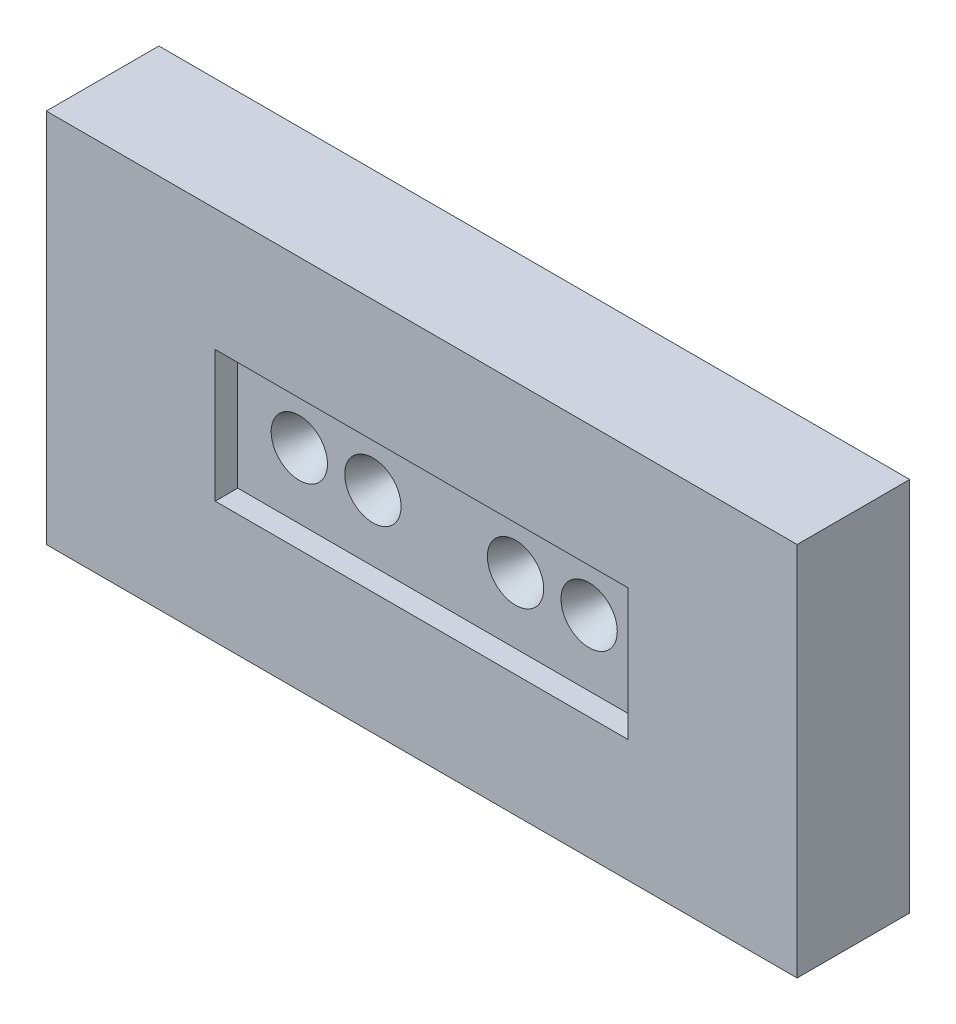
SolidWorks part; units mm, degrees
ref_plane "Front Plane" through (0, 0, 0) normal (0, 0, 1) x (1, 0, 0)
ref_plane "Top Plane" through (0, 0, 0) normal (0, 1, 0) x (1, 0, 0)
ref_plane "Right Plane" through (0, 0, 0) normal (1, 0, 0) x (0, 0, -1)
sketch "Sketch1" plane through (0, 0, 0) normal (0, 0, 1) x (1, 0, 0)
  line L1 (-20, 10) -> (20, 10)
  line L2 (-20, 10) -> (-20, -10)
  line L3 (-20, -10) -> (20, -10)
  line L4 (20, 10) -> (20, -10)
  line L5 (-20, 10) -> (20, -10) construction
  line L6 (-20, -10) -> (20, 10) construction
  point P0 (0, 0)
  dimension "D1" = 40
  dimension "D2" = 20
extrude "Boss-Extrude1" add sketch "Sketch1" along normal blind 6
sketch "Sketch2" plane through (0, 0, 6) normal (0, 0, 1) x (1, 0, 0)
  line L1 (-11, 3.5) -> (11, 3.5)
  line L2 (-11, 3.5) -> (-11, -3.5)
  line L3 (-11, -3.5) -> (11, -3.5)
  line L4 (11, 3.5) -> (11, -3.5)
  line L5 (-11, 3.5) -> (11, -3.5) construction
  line L6 (-11, -3.5) -> (11, 3.5) construction
  point P0 (0, 0)
  dimension "D1" = 22
  dimension "D2" = 7
extrude "Cut-Extrude1" cut sketch "Sketch2" against normal blind 1.2
sketch "Sketch4" plane through (0, 0, 4.8) normal (0, 0, 1) x (1, 0, 0)
  circle A0 centre (-7.72, 0) radius 1.5
  circle A1 centre (-3.8, 0) radius 1.5
  circle A2 centre (3.8, 0) radius 1.5
  circle A3 centre (7.72, 0) radius 1.5
extrude "Cut-Extrude2" cut sketch "Sketch4" against normal blind 2.8 draft 23
sketch "Sketch5" plane through (0, 0, 2) normal (0, 0, 1) x (1, 0, 0)
  circle A0 centre (-7.72, 0) radius 0.3
  circle A1 centre (-3.8, 0) radius 0.3
  circle A2 centre (3.8, 0) radius 0.3
  circle A3 centre (7.72, 0) radius 0.3
extrude "Cut-Extrude3" cut sketch "Sketch5" against normal blind 2.5
